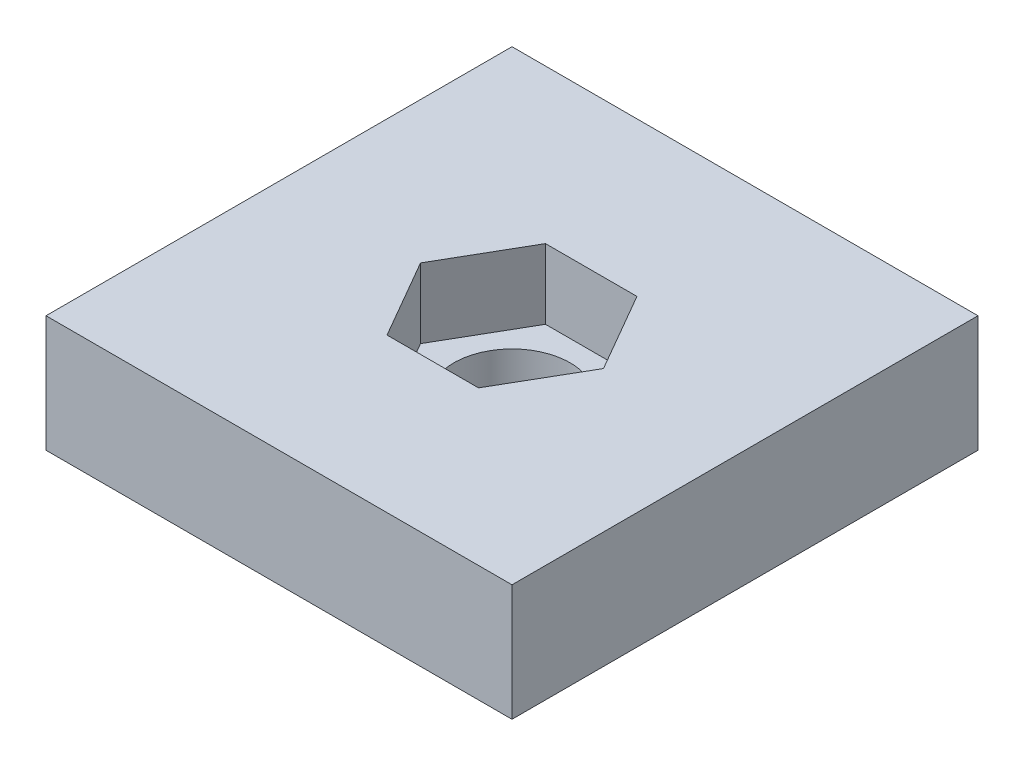
SolidWorks part; units mm, degrees
ref_plane "Front Plane" through (0, 0, 0) normal (0, 0, 1) x (1, 0, 0)
ref_plane "Top Plane" through (0, 0, 0) normal (0, 1, 0) x (1, 0, 0)
ref_plane "Right Plane" through (0, 0, 0) normal (1, 0, 0) x (0, 0, -1)
sketch "Sketch1" plane through (0, 0, 0) normal (0, 1, 0) x (1, 0, 0)
  line L1 (-10, -10) -> (10, -10)
  line L2 (-10, -10) -> (-10, 10)
  line L3 (-10, 10) -> (10, 10)
  line L4 (10, -10) -> (10, 10)
  line L5 (-10, -10) -> (10, 10) construction
  line L6 (-10, 10) -> (10, -10) construction
  point P0 (0, 0)
  dimension "D1" = 20
  dimension "D2" = 20
extrude "Boss-Extrude1" add sketch "Sketch1" along normal blind 5
sketch "Sketch3" plane through (0, 5, 0) normal (0, 1, 0) x (1, 0, 0)
  line L1 (3.926, 0) -> (1.963, 3.4)
  line L2 (1.963, 3.4) -> (-1.963, 3.4)
  line L3 (-1.963, 3.4) -> (-3.926, 0)
  line L4 (-3.926, 0) -> (-1.963, -3.4)
  line L5 (-1.963, -3.4) -> (1.963, -3.4)
  line L6 (1.963, -3.4) -> (3.926, 0)
  circle A0 centre (0, 0) radius 3.4 construction
  dimension "D1" = 6.8
extrude "Cut-Extrude1" cut sketch "Sketch3" against normal blind 3
sketch "Sketch4" plane through (0, 2, 0) normal (0, 1, 0) x (1, 0, 0)
  circle A0 centre (0, 0) radius 2.5
  dimension "D1" = 5
extrude "Cut-Extrude2" cut sketch "Sketch4" against normal through all
equation "\"D2@Sketch1\"=\"D1@Sketch1\""
